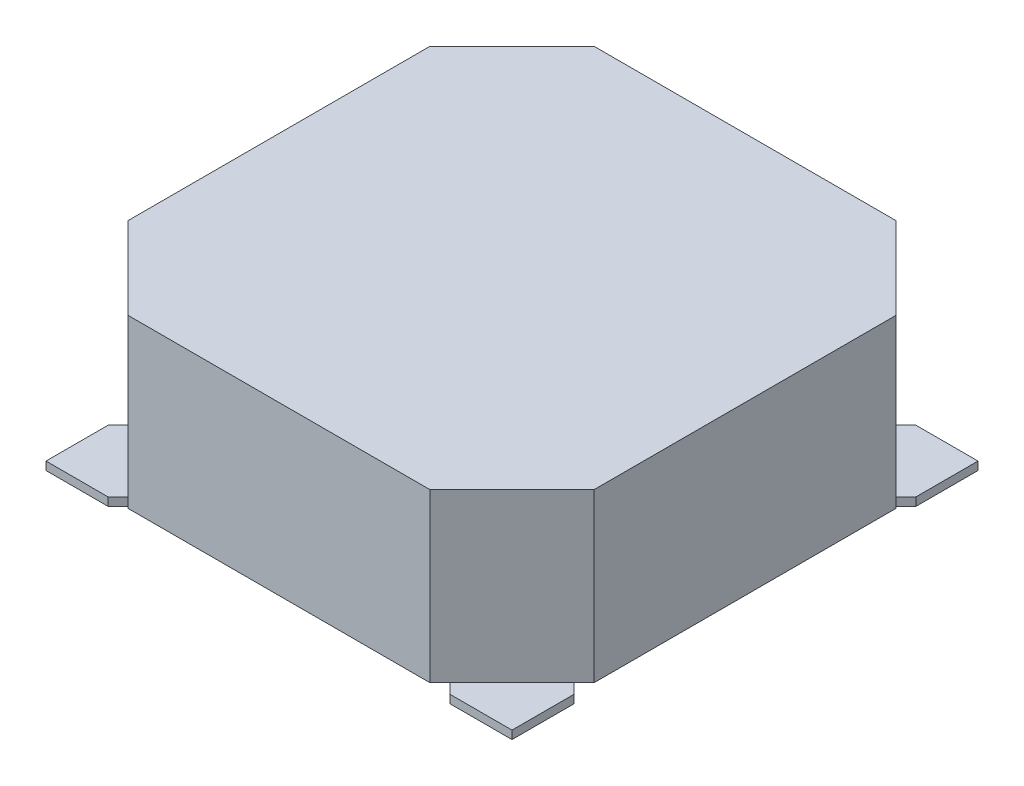
SolidWorks part; units mm, degrees
ref_plane "Front Plane" through (0, 0, 0) normal (0, 0, 1) x (1, 0, 0)
ref_plane "Top Plane" through (0, 0, 0) normal (0, 1, 0) x (1, 0, 0)
ref_plane "Right Plane" through (0, 0, 0) normal (1, 0, 0) x (0, 0, -1)
sketch "Sketch1" plane through (0, 0, 0) normal (0, 1, 0) x (1, 0, 0)
  line L1 (0, 0) -> (8.5, 0)
  line L2 (0, 0) -> (0, -8.5)
  line L3 (0, -8.5) -> (8.5, -8.5)
  line L4 (8.5, 0) -> (8.5, -8.5)
  dimension "D1" = 8.5
  dimension "D2" = 8.5
extrude "Boss-Extrude1" add sketch "Sketch1" along normal blind 3.2
sketch "Sketch2" plane through (0, 3.2, 0) normal (0, 1, 0) x (1, 0, 0)
  line L0 (1.5, 0) -> (0, -1.5)
  line L1 (8.5, -1.5) -> (7, 0)
  line L2 (7, -8.5) -> (8.5, -7)
  line L3 (0, -7) -> (1.5, -8.5)
  line L4 (0, 0) -> (0, -8.5)
  line L5 (0, -8.5) -> (8.5, -8.5)
  line L6 (8.5, -8.5) -> (8.5, 0)
  line L7 (8.5, 0) -> (0, 0)
  line L8 (0, -1.5) -> (0, -7) construction
  line L9 (1.5, -8.5) -> (7, -8.5) construction
  line L10 (8.5, -7) -> (8.5, -1.5) construction
  line L11 (7, 0) -> (1.5, 0) construction
  line L12 (0, -1.5) -> (0, 0)
  line L13 (0, 0) -> (1.5, 0)
  line L14 (1.5, 0) -> (1.5506, 0.09)
  line L15 (7, 0) -> (8.5, 0)
  line L16 (8.5, -8.5) -> (8.5, 0) construction
  line L17 (8.5, 0) -> (0, 0) construction
  line L18 (8.5, 0) -> (8.5, -1.5)
  line L19 (8.5, -7) -> (8.5, -8.5)
  line L20 (8.5, -8.5) -> (7, -8.5)
  line L21 (1.5, -8.5) -> (0, -8.5)
  line L22 (0, -7) -> (0, -8.5)
  line M9 (0, 0) -> (0, -8.5)
  line M10 (0, -8.5) -> (8.5, -8.5)
  line M11 (8.5, -8.5) -> (8.5, 0)
  line M12 (8.5, 0) -> (0, 0)
  dimension "D2" = 1.5
  dimension "D3" = 45
  dimension "D4" = 1.5
  dimension "D5" = 45
  dimension "D6" = 1.5
  dimension "D7" = 45
  dimension "D8" = 1.5
  dimension "D9" = 45
  dimension "D1" = 0
extrude "Cut-Extrude1" cut sketch "Sketch2" against normal blind 3.05 contours L3 M9 M10 | L0 M12 M9 | L1 M11 M12 | L2 M10 M11
sketch "Sketch3" plane through (0, 0, 0) normal (0, -1, 0) x (1, 0, 0)
  line L0 (8.5, 1.1314) -> (7.3686, 0) construction
  line L1 (8.5, 0) -> (0, 0) construction
  line L2 (7.3686, 0) -> (8.5, 0) construction
  line L3 (8.5, 0) -> (8.5, 1.1314) construction
  line L4 (8.5, 8.5) -> (8.5, 0) construction
  line L5 (8.5, 1.1314) -> (7.9697, 1.6617)
  line L6 (7.9697, 1.6617) -> (6.8383, 0.5303)
  line L7 (6.8383, 0.5303) -> (7.3686, 0)
  line L8 (8.5, 8.5) -> (0, 0) construction
  line L9 (8.5, 0) -> (0, 8.5) construction
  line L10 (1.1314, 0) -> (1.6617, 0.5303)
  line L11 (1.6617, 0.5303) -> (0.5303, 1.6617)
  line L12 (0.5303, 1.6617) -> (0, 1.1314)
  line L13 (0, 7.3686) -> (0.5303, 6.8383)
  line L14 (0.5303, 6.8383) -> (1.6617, 7.9697)
  line L15 (1.6617, 7.9697) -> (1.1314, 8.5)
  line L16 (7.3686, 8.5) -> (6.8383, 7.9697)
  line L17 (6.8383, 7.9697) -> (7.9697, 6.8383)
  line L18 (7.9697, 6.8383) -> (8.5, 7.3686)
  line L19 (8.5, 7.3686) -> (8.5, 1.1314)
  line L20 (7.3686, 0) -> (1.1314, 0)
  line L21 (0, 1.1314) -> (0, 7.3686)
  line L22 (1.1314, 8.5) -> (7.3686, 8.5)
  point P16 (4.25, 4.25)
  point P33 (4.25, 4.25)
  dimension "D1" = 1.6
  dimension "D2" = 45
  dimension "D3" = 0.75
  dimension "D4" = 4
extrude "Cut-Extrude2" cut sketch "Sketch3" against normal up to surface (0.15 mm away) up to face at (8, 0.15, 8)
